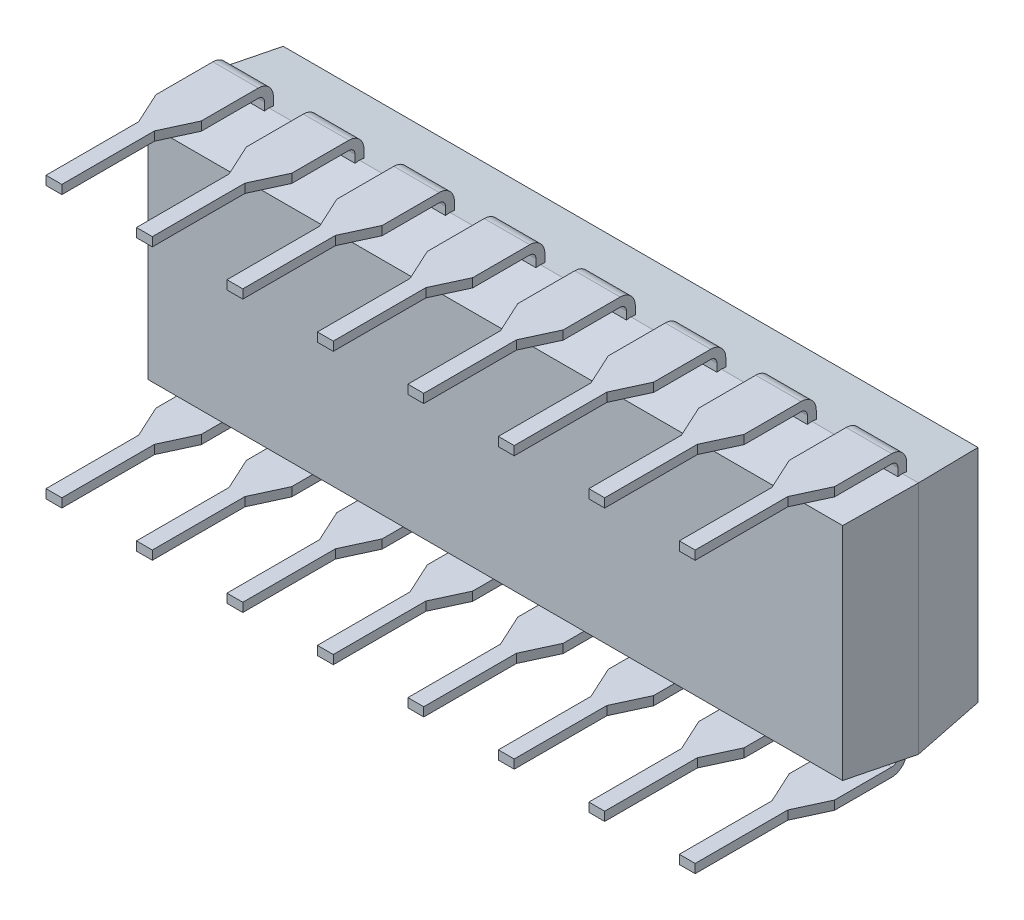
SolidWorks part; units mm, degrees
ref_plane "Plano frontal" through (0, 0, 0) normal (0, 0, 1) x (1, 0, 0)
ref_plane "Plano superior" through (0, 0, 0) normal (0, 1, 0) x (1, 0, 0)
ref_plane "Plano direito" through (0, 0, 0) normal (1, 0, 0) x (0, 0, -1)
sketch "Esboço1" plane through (0, 0, 0) normal (1, 0, 0) x (0, 0, -1)
  line L0 (0.9, 3.1) -> (0.9, -3.1)
  line L1 (0.9, -3.1) -> (2.8, -3.3)
  line L2 (2.8, -3.3) -> (4.7, -3.1)
  line L3 (4.7, -3.1) -> (4.7, 3.1)
  line L4 (4.7, 3.1) -> (2.8, 3.3)
  line L5 (2.8, 3.3) -> (0.9, 3.1)
  line L6 (2.8, 3.3) -> (2.8, -3.3) construction
  line L7 (4.7, 0) -> (2.8, 0) construction
  line L8 (2.8, 0) -> (0.9, 0) construction
  line L9 (0.9, 0) -> (0, 0) construction
  dimension "D1" = 6.6
  dimension "D2" = 6.2
  dimension "D3" = 3.8
  dimension "D4" = 0.9
extrude "Ressalto-extrusão1" add sketch "Esboço1" along normal mid plane 19.96
sketch "Esboço3" plane through (0, 0, 0) normal (0, 1, 0) x (1, 0, 0)
  line L0 (-9.98, 2.8) -> (-9.7499, 4.7268)
  line L1 (-9.7499, 4.7268) -> (-10.9163, 4.7268)
  line L2 (-10.9163, 4.7268) -> (-10.9163, 0.8732)
  line L3 (-10.9163, 0.8732) -> (-9.7499, 0.8732)
  line L4 (-9.7499, 0.8732) -> (-9.98, 2.8)
  line L5 (-10.9163, 2.8) -> (-9.98, 2.8) construction
  line L6 (-9.98, 0.9) -> (-9.98, 2.8) construction
  dimension "D1" = 6.81
  dimension "D2" = 3.8537
  dimension "D3" = 1.1665
extrude "Corte-extrusão2" cut sketch "Esboço3" against normal mid plane 7.1
mirror "Espelhar1" about plane through (0, 0, 0) normal (1, 0, 0) of "Corte-extrusão2"
sketch "Esboço8" plane through (0, 0, -4.7) normal (0, 0, -1) x (-1, 0, 0)
  line L0 (9.7531, -3.1) -> (9.7531, 3.1) construction
  circle A0 centre (9.7531, 0) radius 1
  dimension "D1" = 2
extrude "Corte-extrusão5" cut sketch "Esboço8" against normal blind 0.5
ref_plane "Plano1" through (0, 3.3, 0) normal (0, 1, 0) x (1, 0, 0)
sketch "Esboço6" plane through (0, 3.3, 0) normal (0, 1, 0) x (1, 0, 0)
  line L0 (-8.2525, 2.8) -> (0, 2.8) construction
  line L1 (-9.5275, 2.925) -> (-8.2525, 2.925)
  line L2 (-9.5275, 2.925) -> (-9.5275, 2.675)
  line L3 (-9.5275, 2.675) -> (-8.2525, 2.675)
  line L4 (-8.2525, 2.925) -> (-8.2525, 2.675)
  line L5 (9.98, 2.8) -> (-9.98, 2.8) construction
  line L6 (-8.89, 2.925) -> (-8.89, 2.675) construction
  dimension "D1" = 0.25
  dimension "D2" = 1.275
  dimension "D3" = 1.09
extrude "Ressalto-extrusão2" add sketch "Esboço6" along normal mid plane 0.05
sketch "Esboço7" plane through (0, 3.325, 0) normal (0, 1, 0) x (1, 0, 0)
  line L0 (-9.5275, 2.925) -> (-9.5275, 2.675) construction
  line L1 (-8.2525, 2.925) -> (-9.5275, 2.925) construction
  line L2 (-8.2525, 2.675) -> (-8.2525, 2.925) construction
  line L3 (-9.5275, 2.675) -> (-8.2525, 2.675) construction
  line L4 (-9.5275, 2.925) -> (-9.5275, 2.675)
  line L5 (-8.2525, 2.925) -> (-9.5275, 2.925)
  line L6 (-8.2525, 2.675) -> (-8.2525, 2.925)
  line L7 (-9.5275, 2.675) -> (-8.2525, 2.675)
  line L8 (-9.5275, 2.8) -> (-8.2525, 2.8) construction
sketch3d "3DSketch1"
  line L0 (-8.89, 3.325, -2.8) -> (-8.89, 3.51, -2.8)
  line L1 (-8.89, 3.325, -2.8) -> (-8.89, 0, -2.8) construction
  line L2 (-9.5275, 3.325, -2.8) -> (-8.2525, 3.325, -2.8) construction
  line L3 (-8.89, 3.81, -2.5) -> (-8.89, 3.81, 0)
  line L4 (-8.89, 0, -2.8) -> (0, 0, 0) construction
  arc A0 (-8.89, 3.51, -2.8) -> (-8.89, 3.81, -2.5) centre (-8.89, 3.51, -2.5) ccw
  point P5 (-8.59, 3.51, -2.5)
  dimension "D3" = 0.3
  dimension "D1" = 2.8
  dimension "D2" = 3.81
sweep "Varredura1" add profiles "Esboço7" path "3DSketch1"
sketch "Esboço9" plane through (0, 3.935, 0) normal (0, 1, 0) x (1, 0, 0)
  line L0 (-9.1125, 0) -> (-9.5275, 0.9)
  line L1 (-8.2525, 0) -> (-9.5275, 0) construction
  line L3 (-9.5275, 2.5) -> (-9.5275, 0) construction
  line L4 (-9.5275, 0.9) -> (-9.5275, -0.2)
  line L5 (-9.5275, -0.2) -> (-8.2525, -0.2)
  line L6 (-8.2525, -0.2) -> (-8.2525, 0.9)
  line L7 (-8.2525, 2.5) -> (-8.2525, 0) construction
  line L8 (-8.2525, 0.9) -> (-8.6675, 0)
  line L9 (-8.6675, 0) -> (-9.1125, 0)
  line L10 (-8.89, 0) -> (-8.89, 2.5) construction
  line L11 (-8.2525, 2.5) -> (-9.5275, 2.5) construction
  dimension "D1" = 0.9
  dimension "D2" = 0.445
  dimension "D3" = 0.2
extrude "Corte-extrusão6" cut sketch "Esboço9" against normal up to next (0.25 mm away)
sketch "Esboço10" plane through (0, 0, 0) normal (0, 0, 1) x (1, 0, 0)
  line L0 (-8.6675, 3.935) -> (-9.1125, 3.935) construction
  line L1 (-9.1125, 3.935) -> (-9.1125, 3.685) construction
  line L2 (-9.1125, 3.685) -> (-8.6675, 3.685) construction
  line L3 (-8.6675, 3.685) -> (-8.6675, 3.935) construction
  line L4 (-8.6675, 3.935) -> (-9.1125, 3.935)
  line L5 (-9.1125, 3.935) -> (-9.1125, 3.685)
  line L6 (-9.1125, 3.685) -> (-8.6675, 3.685)
  line L7 (-8.6675, 3.685) -> (-8.6675, 3.935)
extrude "Ressalto-extrusão3" add sketch "Esboço10" along normal blind 2.6
mirror "Espelhar2" about plane through (0, 0, 0) normal (0, 1, 0) of "Ressalto-extrusão3", "Corte-extrusão6", "Varredura1", "Ressalto-extrusão2"
pattern_linear "Padrão linear1" count 8 spacing 2.54 along (1, 0, 0) of "Ressalto-extrusão2", "Varredura1", "Corte-extrusão6", "Ressalto-extrusão3", "Espelhar2"
